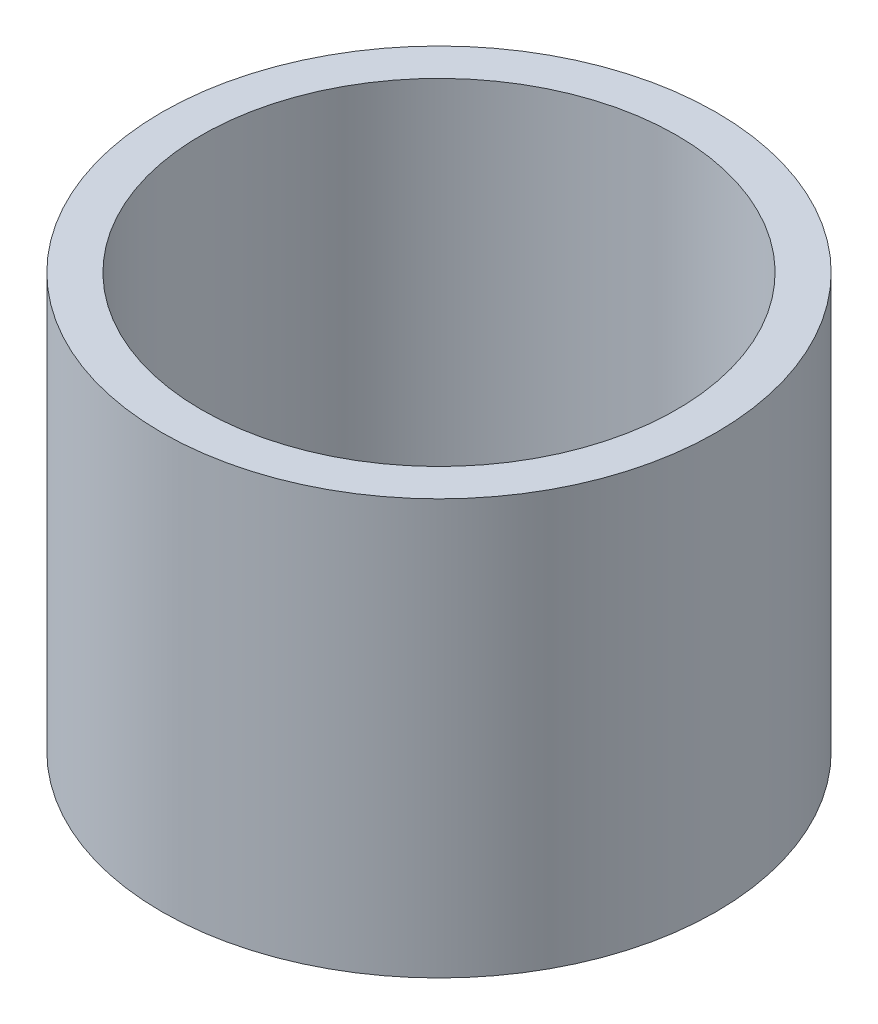
SolidWorks part; units mm, degrees
ref_plane "Front Plane" through (0, 0, 0) normal (0, 0, 1) x (1, 0, 0)
ref_plane "Top Plane" through (0, 0, 0) normal (0, 1, 0) x (1, 0, 0)
ref_plane "Right Plane" through (0, 0, 0) normal (1, 0, 0) x (0, 0, -1)
sketch "Sketch1" plane through (0, 0, 0) normal (0, 1, 0) x (1, 0, 0)
  circle A0 centre (0, 0) radius 25.775
  circle A1 centre (0, 0) radius 30.075
extrude "Boss-Extrude1" add sketch "Sketch1" along normal blind 45
